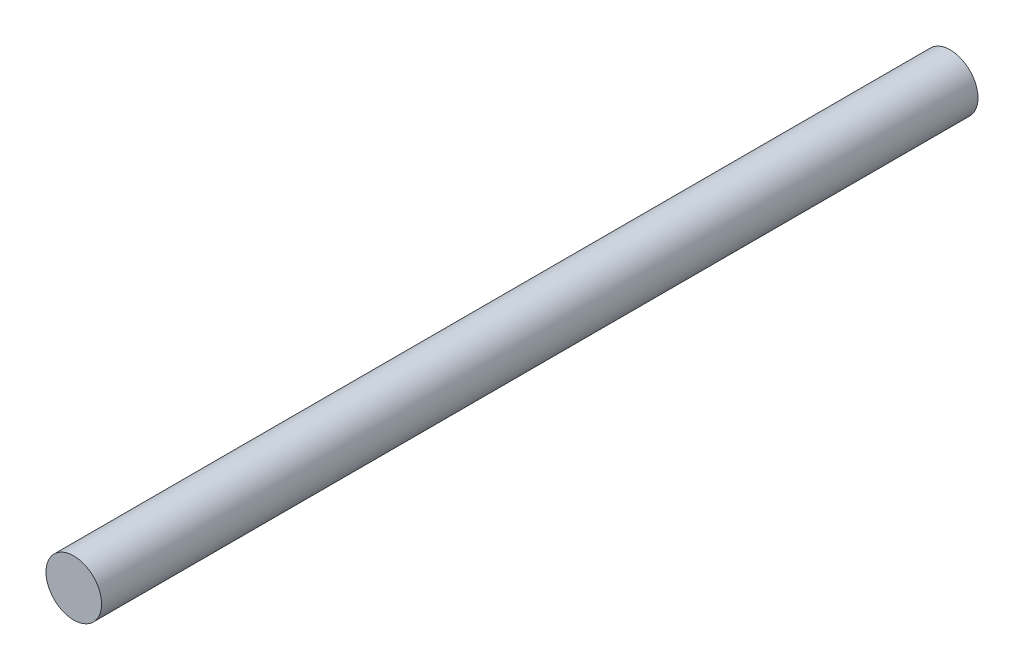
SolidWorks part; units mm, degrees
ref_plane "Plan de face" through (0, 0, 0) normal (0, 0, 1) x (1, 0, 0)
ref_plane "Plan de dessus" through (0, 0, 0) normal (0, 1, 0) x (1, 0, 0)
ref_plane "Plan de droite" through (0, 0, 0) normal (1, 0, 0) x (0, 0, -1)
sketch "Esquisse2" plane through (0, 0, 0) normal (0, 0, 1) x (1, 0, 0)
  circle A0 centre (0, 0) radius 2.95
  dimension "D1" = 5.9
extrude "Boss.-Extru.1" add sketch "Esquisse2" along normal blind 93
